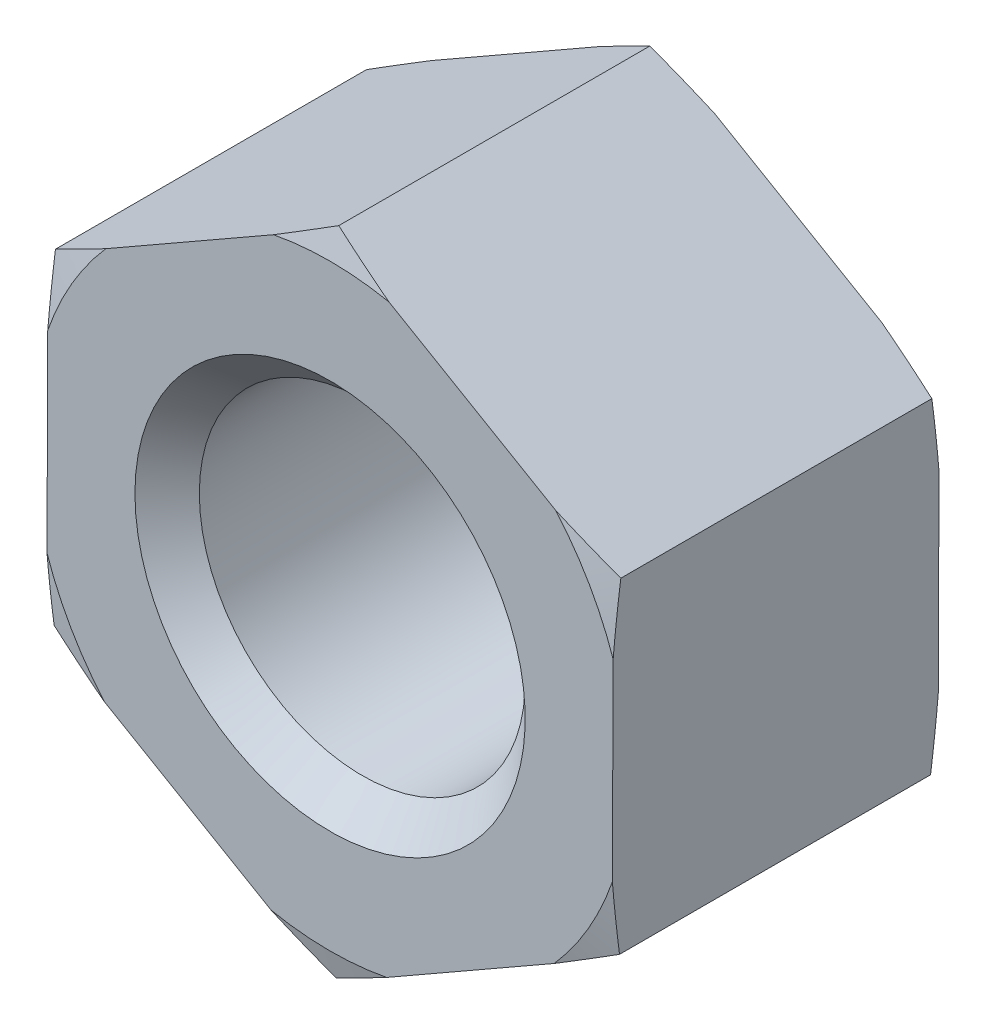
SolidWorks part; units mm, degrees
extrude "基体-拉伸" add sketch "草图1" along normal blind 3
sketch "草图1" plane through (0, 0, 0) normal (0, 0, 1) x (1, 0, 0)
  line L0 (-26.8088, 0) -> (37.1748, 0) construction
  line L1 (0, 25.0215) -> (0, -25.0215) construction
  line L3 (0.0118, 3.005) -> (-2.5965, 1.5127)
  line L4 (-2.5965, 1.5127) -> (-2.6083, -1.4923)
  line L5 (-2.6083, -1.4923) -> (-0.0118, -3.005)
  line L6 (-0.0118, -3.005) -> (2.5965, -1.5127)
  line L7 (2.5965, -1.5127) -> (2.6083, 1.4923)
  line L8 (2.6083, 1.4923) -> (0.0118, 3.005)
  circle A0 centre (0, 0) radius 2.6024 construction
  circle A1 centre (0, 0) radius 1.5
  dimension "D" = 3
  dimension "e" = 6.01
cosmetic thread "装饰螺纹线1"
chamfer "倒角1" distance 0.2964 angle 45 2 edges at (1.5, 0, 0) (1.5, 0, 3)
material "04级"
ref_plane "基准面1" through (0, 0, 0) normal (0, 0, 1) x (1, 0, 0)
ref_plane "基准面2" through (0, 0, 0) normal (0, 1, 0) x (1, 0, 0)
ref_plane "基准面3" through (0, 0, 0) normal (1, 0, 0) x (0, 0, -1)
sketch "尺寸草图" plane through (0, 0, 0) normal (0, 0, 1) x (1, 0, 0)
  line L0 (0, 0) -> (24.1005, 0)
  line L1 (0, 0) -> (3.45, 0)
  line L2 (46.8781, 0) -> (51.4781, 0)
  line L3 (-2.8571, 0) -> (0, 0)
  point P3 (3, 0)
  point P4 (2.5, 0)
  point P5 (6.01, 0)
  point P6 (1.8, 0)
  point P7 (7.3, 0)
  point P8 (5.5, 0)
  dimension "D" = 3
  dimension "e" = 6.01
  dimension "P" = 2.5
  dimension "m" = 1.8
  dimension "mw" = 7.3
  dimension "s" = 5.5
  dimension "da" = 3.45
  dimension "dw" = 4.6
  dimension "D1" = 2.8571
sketch "草图2" plane through (0, 0, 0) normal (0, 0, -1) x (-1, 0, 0)
  circle A0 centre (0, 0) radius 2.75
  circle A1 centre (0, 0) radius 1.5 construction
  dimension "s" = 5.5
extrude "切除-拉伸1" cut sketch "草图2" against normal through all draft 75 flip side to cut
sketch "草图3" plane through (0, 0, 3) normal (0, 0, 1) x (1, 0, 0)
  circle A0 centre (0, 0) radius 2.75
  dimension "D1" = 5.5
extrude "切除-拉伸2" cut sketch "草图3" against normal through all draft 75 flip side to cut
equation "\"e@草图1\" = \"e@尺寸草图\""
equation "\"D1@尺寸草图\" = \"D@尺寸草图\" / 1.05"
equation "\"D@草图1\" = \"D@尺寸草图\""
equation "\"D1@草图3\" = \"s@尺寸草图\""
equation "\"s@草图2\" = \"s@尺寸草图\""
equation "\"D2@装饰螺纹线1\" = 1.05 * \"D1@尺寸草图\""
equation "\"D1@倒角1\" =  ( \"da@尺寸草图\" - \"D1@尺寸草图\" )  / 2"
